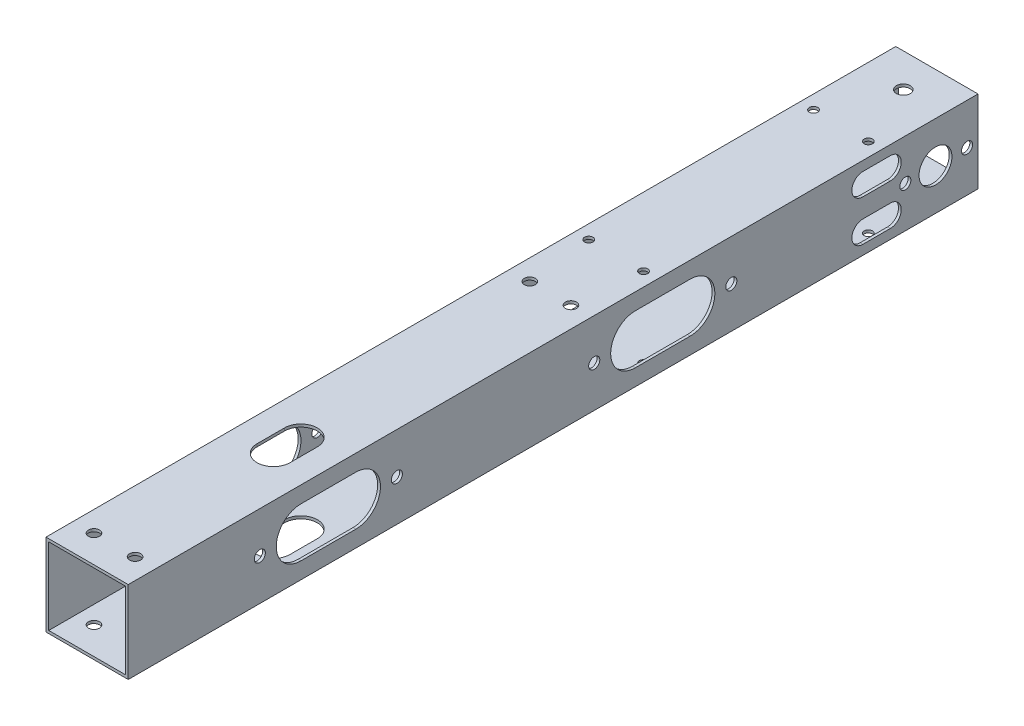
SolidWorks part; units mm, degrees
material "6063-T5"
ref_plane "前视基准面" through (0, 0, 0) normal (0, 0, 1) x (1, 0, 0)
ref_plane "上视基准面" through (0, 0, 0) normal (0, 1, 0) x (1, 0, 0)
ref_plane "右视基准面" through (0, 0, 0) normal (1, 0, 0) x (0, 0, -1)
other "Configuration Table"
sketch "草图1" plane through (0, 0, 0) normal (0, 0, 1) x (1, 0, 0)
  line L1 (-15, -15) -> (15, -15)
  line L2 (-15, -15) -> (-15, 15)
  line L3 (-15, 15) -> (15, 15)
  line L4 (15, -15) -> (15, 15)
  line L5 (-15, -15) -> (15, 15) construction
  line L6 (-15, 15) -> (15, -15) construction
  point P0 (0, 0)
  dimension "D1" = 30
  dimension "D2" = 30
extrude "凸台-拉伸1" add sketch "草图1" along normal mid plane 310
sketch "草图2" plane through (0, 0, 0) normal (0, 0, 1) x (1, 0, 0)
  line L8 (14, -14) -> (14, 14)
  line L9 (14, 14) -> (-14, 14)
  line L10 (-14, 14) -> (-14, -14)
  line L11 (-14, -14) -> (14, -14)
  line L12 (14, -14) -> (14, 14)
  line L13 (14, 14) -> (-14, 14)
  line L14 (-14, 14) -> (-14, -14)
  line L15 (-14, -14) -> (14, -14)
  dimension "D1" = 1
extrude "切除-拉伸1" cut sketch "草图2" against normal through all both and the other way through all
sketch "草图3" plane through (-15, 0, 0) normal (-1, 0, 0) x (0, 0, 1)
  circle A0 centre (-151, 0) radius 2.025
  circle A1 centre (-128.5, 0) radius 2.025
  dimension "D1" = 4.05
extrude "切除-拉伸2" cut sketch "草图3" against normal through all
sketch "草图4" plane through (-15, 0, 0) normal (-1, 0, 0) x (0, 0, 1)
  line L0 (155, 15) -> (-155, 15) construction
  line L1 (155, 15) -> (155, -15) construction
  circle A0 centre (-65, 0) radius 2.025
  circle A1 centre (-15, 0) radius 2.025
  circle A2 centre (107, 0) radius 2.025
  circle A3 centre (57, 0) radius 2.025
  dimension "D1" = 4.05
  dimension "D2" = 50
  dimension "D3" = 15
  dimension "D4" = 15
  dimension "D5" = 48
  dimension "D6" = 50
  dimension "D7" = 72
extrude "切除-拉伸3" cut sketch "草图4" against normal through all both and the other way through all
sketch "草图5" plane through (0, -15, 0) normal (0, -1, 0) x (1, 0, 0)
  line L0 (-15, 155) -> (15, 155) construction
  line L1 (0, 155) -> (0, 145) construction
  line L2 (0, 145) -> (7.5, 145) construction
  circle A4 centre (-7.5, 145) radius 2.025
  circle A5 centre (7.5, 145) radius 2.025
  dimension "D1" = 4.05
  dimension "D2" = 15
  dimension "D3" = 10
extrude "切除-拉伸4" cut sketch "草图5" against normal through all both
sketch "草图6" plane through (0, -15, 0) normal (0, -1, 0) x (1, 0, 0)
  line L0 (-15, 155) -> (-15, -155) construction
  line L1 (10, -24) -> (-10, -24)
  line L2 (10, -24) -> (10, -4)
  line L3 (10, -4) -> (-10, -4)
  line L4 (-10, -24) -> (-10, -4)
  line L5 (10, -24) -> (-10, -4) construction
  line L6 (10, -4) -> (-10, -24) construction
  line L7 (334.5, -4) -> (-65.5, -4) construction
  point P0 (0, -14)
  dimension "D1" = 20
  dimension "D2" = 5
  dimension "D3" = 20
extrude "切除-拉伸5" cut sketch "草图6" against normal blind 3
fillet "圆角1" radius 2 4 edges at (10, -14.5, -24) (-10, -14.5, -24) (-10, -14.5, -4) (10, -14.5, -4)
sketch "草图7" plane through (0, 15, 0) normal (0, 1, 0) x (1, 0, 0)
  circle A0 centre (-7.5, 14) radius 2.025
  circle A1 centre (7.5, 14) radius 2.025
  dimension "D1" = 4.05
extrude "切除-拉伸6" cut sketch "草图7" against normal through all both and the other way through all
sketch "草图8" plane through (-15, 0, 0) normal (-1, 0, 0) x (0, 0, 1)
  line L0 (-147, 0) -> (-132, 0) construction
  line L1 (-147, 5) -> (-147, -5) construction
  line L2 (-132, -5) -> (-132, 5) construction
  circle A0 centre (-139.5, 0) radius 6
  dimension "D1" = 12
extrude "切除-拉伸7" cut sketch "草图8" against normal through all both
sketch "草图9" plane through (0, 15, 0) normal (0, 1, 0) x (1, 0, 0)
  line L0 (-15, -155) -> (-15, 155) construction
  line L1 (15, -155) -> (15, 155) construction
  line L2 (15, 155) -> (-15, 155) construction
  circle A0 centre (-10, 120) radius 1.525
  circle A1 centre (10, 120) radius 1.525
  circle A2 centre (-10, 38) radius 1.525
  circle A3 centre (10, 38) radius 1.525
  dimension "D1" = 3.05
  dimension "D2" = 5
  dimension "D3" = 20
  dimension "D4" = 5
  dimension "D5" = 35
  dimension "D6" = 20
  dimension "D7" = 5
  dimension "D8" = 5
  dimension "D9" = 82
extrude "切除-拉伸8" cut sketch "草图9" against normal through all
sketch "草图10" plane through (-15, 0, 0) normal (-1, 0, 0) x (0, 0, 1)
  line L0 (-50, 0) -> (-30, 0) construction
  line L1 (-50, 9) -> (-30, 9)
  line L2 (-50, -9) -> (-30, -9)
  arc A0 (-50, 9) -> (-50, -9) centre (-50, 0) ccw
  arc A1 (-30, -9) -> (-30, 9) centre (-30, 0) ccw
  point P2 (-40, 0)
  dimension "D2" = 20
  dimension "D1" = 18
  dimension "D3" = 40
extrude "切除-拉伸9" cut sketch "草图10" against normal through all
sketch "草图11" plane through (-15, 0, 0) normal (-1, 0, 0) x (0, 0, 1)
  line L0 (-123, 7.5) -> (-113, 7.5) construction
  line L1 (-123, 11.5) -> (-113, 11.5)
  line L2 (-123, 3.5) -> (-113, 3.5)
  line L3 (-123, -7.5) -> (-113, -7.5) construction
  line L4 (-123, -3.5) -> (-113, -3.5)
  line L5 (-123, -11.5) -> (-113, -11.5)
  line L6 (0, 0) -> (-15, 0)
  line L7 (155, 15) -> (-155, 15) construction
  line L9 (-155, 15) -> (-155, -15) construction
  arc A0 (-123, 11.5) -> (-123, 3.5) centre (-123, 7.5) ccw
  arc A1 (-113, 3.5) -> (-113, 11.5) centre (-113, 7.5) ccw
  arc A2 (-123, -3.5) -> (-123, -11.5) centre (-123, -7.5) ccw
  arc A3 (-113, -11.5) -> (-113, -3.5) centre (-113, -7.5) ccw
  point P2 (-118, 7.5)
  point P7 (-118, -7.5)
  dimension "D1" = 4
  dimension "D2" = 15
  dimension "D3" = 3.5
  dimension "D4" = 10
  dimension "D5" = 32
extrude "切除-拉伸10" cut sketch "草图11" against normal through all contours L2 A1 L1 A0 | L5 A3 L4 A2
sketch "草图12" plane through (-15, 0, 0) normal (-1, 0, 0) x (0, 0, 1)
  line L0 (72, 0) -> (92, 0) construction
  line L1 (72, 9) -> (92, 9)
  line L2 (72, -9) -> (92, -9)
  line L3 (155, 15) -> (155, -15) construction
  arc A0 (72, 9) -> (72, -9) centre (72, 0) ccw
  arc A1 (92, -9) -> (92, 9) centre (92, 0) ccw
  arc A2 (-30, -9) -> (-30, 9) centre (-30, 0) ccw construction
  point P2 (82, 0)
  dimension "D1" = 73
  dimension "D2" = 20
extrude "切除-拉伸11" cut sketch "草图12" against normal through all both and the other way through all
sketch "草图13" plane through (0, 15, 0) normal (0, 1, 0) x (1, 0, 0)
  line L0 (0, -82) -> (0, 0) construction
  line L1 (15, -155) -> (-15, -155) construction
  line L2 (0, -87) -> (0, -77) construction
  line L3 (-6, -87) -> (-6, -77)
  line L4 (6, -87) -> (6, -77)
  circle A0 centre (0, -82) radius 5.025 construction
  arc A1 (-6, -87) -> (6, -87) centre (0, -87) ccw
  arc A2 (6, -77) -> (-6, -77) centre (0, -77) ccw
  point P8 (0, -82)
  dimension "D1" = 10.05
  dimension "D2" = 73
  dimension "D4" = 6
  dimension "D3" = 10
extrude "切除-拉伸12" cut sketch "草图13" along normal through all both and the other way through all from surface at -29 starting at face at (10, -14, -121.525)
sketch "草图14" plane through (0, 15, 0) normal (0, 1, 0) x (1, 0, 0)
  line L0 (15, 155) -> (-15, 155) construction
  line L1 (15, -155) -> (15, 155) construction
  circle A0 centre (0, 142.75) radius 2.525
  dimension "D1" = 5.05
  dimension "D3" = 15
  dimension "D2" = 12.25
extrude "切除-拉伸13" cut sketch "草图14" against normal up to next
